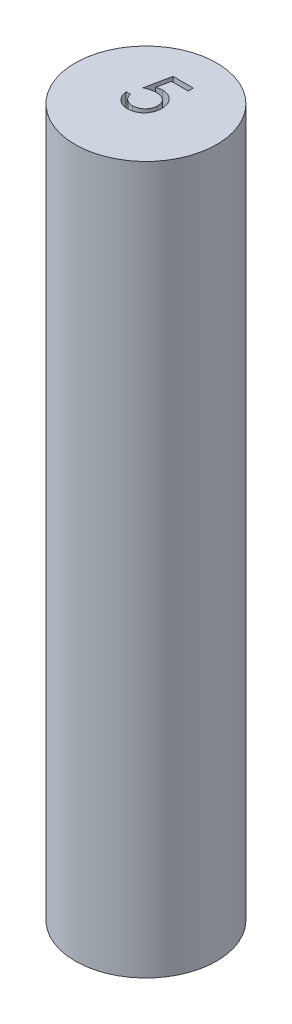
SolidWorks part; units mm, degrees
ref_plane "Front Plane" through (0, 0, 0) normal (0, 0, 1) x (1, 0, 0)
ref_plane "Top Plane" through (0, 0, 0) normal (0, 1, 0) x (1, 0, 0)
ref_plane "Right Plane" through (0, 0, 0) normal (1, 0, 0) x (0, 0, -1)
sketch "Sketch1" plane through (0, 0, 0) normal (0, 1, 0) x (1, 0, 0)
  circle A0 centre (0, 0) radius 5
  dimension "D1" = 10
extrude "Boss-Extrude1" add sketch "Sketch1" along normal blind 50
sketch "Sketch2" plane through (0, 50, 0) normal (0, 1, 0) x (1, 0, 0)
  line L0 (-4.2243, -0.8681) -> (3.6872, -0.8681) construction
  text T0 "5"
extrude "Cut-Extrude1" cut sketch "Sketch2" against normal blind 3
